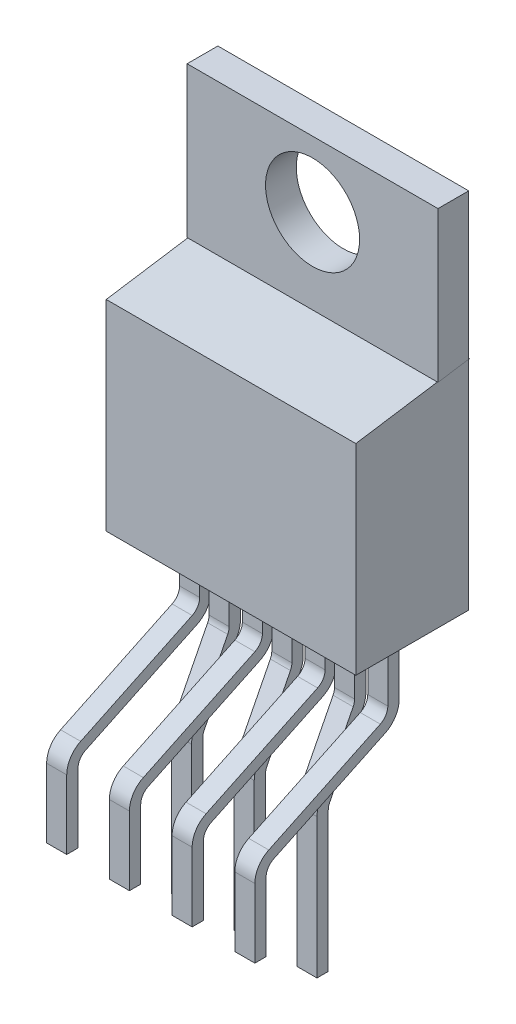
SolidWorks part; units mm, degrees
ref_plane "Front Plane" through (0, 0, 0) normal (0, 0, 1) x (1, 0, 0)
ref_plane "Top Plane" through (0, 0, 0) normal (0, 1, 0) x (1, 0, 0)
ref_plane "Right Plane" through (0, 0, 0) normal (1, 0, 0) x (0, 0, -1)
ref_plane "Plane2" through (0, 0, 1.397) normal (0, 0, 1) x (1, 0, 0)
ref_plane "Plane3" through (0, 6.35, 0) normal (0, 1, 0) x (-1, 0, 0)
ref_plane "Plane4" through (2.54, 0, 0) normal (1, 0, 0) x (0, 0, -1)
sketch "Sketch2" plane through (0, 6.35, 0) normal (0, 1, 0) x (-1, 0, 0)
  line L1 (1.27, -7.5946) -> (-8.89, -7.5946)
  line L2 (1.27, -7.5946) -> (1.27, -3.0226)
  line L3 (1.27, -3.0226) -> (-8.89, -3.0226)
  line L4 (-8.89, -7.5946) -> (-8.89, -3.0226)
  dimension "D1" = 10.16
  dimension "D2" = 4.572
  dimension "D3" = 1.27
  dimension "D4" = 7.5946
extrude "Base-Extrude" add sketch "Sketch2" along normal blind 14.732
sketch "Sketch3" plane through (-1.27, 0, 0) normal (-1, 0, 0) x (0, 0, 1)
  line L0 (-6.3246, 14.986) -> (-6.3246, 21.082)
  line L1 (-6.3246, 14.986) -> (-3.0226, 14.478)
  line L2 (-7.5946, 21.082) -> (-7.5946, 6.35) construction
  line L3 (-7.5946, 21.082) -> (-3.0226, 21.082) construction
  line L5 (-3.0226, 21.082) -> (-3.0226, 6.35) construction
  dimension "D1" = 1.27
  dimension "D2" = 6.096
  dimension "D3" = 6.604
extrude "Cut-Extrude1" cut sketch "Sketch3" against normal through all and the other way through all
sketch "Sketch5" plane through (-1.27, 0, 0) normal (-1, 0, 0) x (0, 0, 1)
  line L0 (-6.3246, 14.986) -> (-3.0226, 14.478) construction
  line L1 (-7.5946, 21.082) -> (-7.5946, 6.35) construction
  line L2 (-7.5946, 6.35) -> (-3.0226, 6.35) construction
  line L3 (-3.0226, 14.478) -> (-3.0226, 6.35) construction
  line L4 (-7.5946, 15.1814) -> (-3.0226, 14.478)
  line L5 (-7.5946, 15.1814) -> (-7.5946, 6.35)
  line L6 (-7.5946, 6.35) -> (-3.0226, 6.35)
  line L7 (-3.0226, 14.478) -> (-3.0226, 6.35)
extrude "Cut-Extrude4" cut sketch "Sketch5" against normal blind 0.0254
sketch "Sketch6" plane through (8.89, 0, 0) normal (1, 0, 0) x (0, 0, -1)
  line L0 (3.0226, 14.478) -> (6.3246, 14.986) construction
  line L1 (3.0226, 14.478) -> (3.0226, 6.35) construction
  line L2 (3.0226, 6.35) -> (7.5946, 6.35) construction
  line L3 (7.5946, 21.082) -> (7.5946, 6.35) construction
  line L4 (3.0226, 14.478) -> (7.5946, 15.1814)
  line L5 (3.0226, 14.478) -> (3.0226, 6.35)
  line L6 (3.0226, 6.35) -> (7.5946, 6.35)
  line L7 (7.5946, 15.1814) -> (7.5946, 6.35)
extrude "Cut-Extrude5" cut sketch "Sketch6" against normal blind 0.0254
sketch "Sketch7" plane through (0, 0, -7.5946) normal (0, 0, -1) x (-1, 0, 0)
  line L0 (-8.89, 21.082) -> (-8.89, 15.1814) construction
  line L1 (-8.89, 21.082) -> (1.27, 21.082) construction
  line L2 (1.27, 21.082) -> (1.27, 15.1814) construction
  line L3 (-8.89, 21.082) -> (-8.89, 15.1814)
  line L4 (-8.89, 21.082) -> (1.27, 21.082)
  line L5 (1.27, 21.082) -> (1.27, 15.1814)
  line L6 (-8.89, 15.1814) -> (-7.62, 15.1814)
  line L7 (-7.62, 15.1814) -> (-7.62, 9.652)
  line L8 (-7.62, 9.652) -> (0, 9.652)
  line L9 (0, 15.1814) -> (0, 9.652)
  line L10 (0, 15.1814) -> (1.27, 15.1814)
  line L11 (-8.8646, 6.35) -> (-8.8646, 15.1814) construction
  line L12 (-8.8646, 6.35) -> (1.2446, 6.35) construction
  line L13 (1.2446, 15.1814) -> (1.2446, 6.35) construction
  dimension "D1" = 1.2446
  dimension "D2" = 3.302
  dimension "D3" = 1.2446
extrude "Cut-Extrude6" cut sketch "Sketch7" against normal blind 0.0254
sketch "Sketch9" plane through (0, 0, 0) normal (1, 0, 0) x (0, 0, -1)
  line L0 (0, 0.254) -> (0, -2.54)
  line L2 (5.3848, 6.35) -> (5.3848, 3.7846)
  line L3 (50, 6.35) -> (-50, 6.35) construction
  line L4 (4.9509, 3.0969) -> (0.4339, 0.9417)
  arc A0 (4.9509, 3.0969) -> (5.3848, 3.7846) centre (4.6228, 3.7846) ccw
  arc A1 (0.4339, 0.9417) -> (0, 0.254) centre (0.762, 0.254) ccw
  dimension "D1" = 0.762
  dimension "D2" = 5.3848
  dimension "D3" = 2.5654
  dimension "D4" = 6.096
  dimension "D5" = 2.54
extrude "Boss-Extrude-Thin1" add sketch "Sketch9" along normal mid plane 0.8128 thin thin type two direction wall 0.2286 second wall 0.2286
pattern_linear "LPattern2" count 4 spacing 2.54 along (1, 0, 0) of "Boss-Extrude-Thin1"
ref_plane "Plane5" through (1.27, 0, 0) normal (1, 0, 0) x (0, 0, -1)
sketch "Sketch10" plane through (1.27, 0, 0) normal (1, 0, 0) x (0, 0, -1)
  line L0 (5.3086, 6.35) -> (5.3086, 3.4338)
  line L1 (50, 6.35) -> (-50, 6.35) construction
  line L2 (5.2258, 3.0884) -> (3.8674, 0.4168)
  line L3 (3.7846, 0.0714) -> (3.7846, -5.588)
  line L4 (7.5946, 6.35) -> (3.0226, 6.35) construction
  arc A0 (5.2258, 3.0884) -> (5.3086, 3.4338) centre (4.5466, 3.4338) ccw
  arc A1 (3.8674, 0.4168) -> (3.7846, 0.0714) centre (4.5466, 0.0714) ccw
  point P10 (5.3086, 3.2512)
  point P13 (3.7846, 0.254)
  dimension "D5" = 0.762
  dimension "D1" = 1.524
  dimension "D2" = 11.938
  dimension "D3" = 5.842
  dimension "D4" = 3.0988
extrude "Boss-Extrude-Thin2" add sketch "Sketch10" along normal mid plane 0.8128 thin thin type two direction wall 0.2286 second wall 0.2286
pattern_linear "LPattern3" count 3 spacing 2.54 along (1, 0, 0) of "Boss-Extrude-Thin2"
sketch "Sketch4" plane through (0, 0, -6.3246) normal (0, 0, 1) x (1, 0, 0)
  line L1 (-1.27, 21.082) -> (8.89, 21.082) construction
  line L2 (3.81, 21.082) -> (3.81, 8.7865) construction
  circle A0 centre (3.81, 18.415) radius 1.905
  dimension "D1" = 3.81
  dimension "D2" = 2.667
extrude "Cut-Extrude2" cut sketch "Sketch4" against normal blind 14.732
sketch "Component_Outline" plane through (0, 0, 0) normal (0, 1, 0) x (1, 0, 0)
  line L0 (-1.2446, 3.0226) -> (8.8646, 3.0226) construction
  line L2 (0.4064, -0.2286) -> (0.4064, 3.0226)
  line L3 (0.4064, 3.0226) -> (2.1336, 3.0226)
  line L4 (2.1336, -0.2286) -> (2.1336, 3.0226)
  line L5 (2.1336, 5.0494) -> (2.1336, 0.5323) construction
  line L6 (4.6736, 5.0494) -> (4.6736, 0.5323) construction
  line L8 (2.9464, -0.2286) -> (2.9464, 3.0226)
  line L9 (2.9464, 3.0226) -> (4.6736, 3.0226)
  line L10 (4.6736, -0.2286) -> (4.6736, 3.0226)
  line L11 (7.2136, 5.0494) -> (7.2136, 0.5323) construction
  line L13 (5.4864, -0.2286) -> (5.4864, 3.0226)
  line L14 (5.4864, 3.0226) -> (7.2136, 3.0226)
  line L15 (7.2136, -0.2286) -> (7.2136, 3.0226)
  line L16 (-0.4064, 3.0226) -> (-1.2446, 3.0226)
  line L17 (-0.4064, 5.0494) -> (-0.4064, 0.5323) construction
  line L18 (-1.2446, 3.0226) -> (-1.27, 7.5946)
  line L19 (-1.27, 7.5946) -> (8.8646, 7.5946)
  line L20 (8.8646, 7.5946) -> (8.8646, 3.0226)
  line L21 (8.8646, 3.0226) -> (8.0264, 3.0226)
  line L22 (8.0264, 5.0494) -> (8.0264, 0.5323) construction
  line L23 (8.0264, 3.0226) -> (8.0264, -0.2286)
  line L24 (8.0264, -0.2286) -> (7.2136, -0.2286)
  line L25 (-0.4064, -0.2286) -> (-0.4064, 3.0226)
  line L26 (0.4064, -0.2286) -> (-0.4064, -0.2286)
  line L27 (2.9464, -0.2286) -> (2.1336, -0.2286)
  line L28 (5.4864, -0.2286) -> (4.6736, -0.2286)
